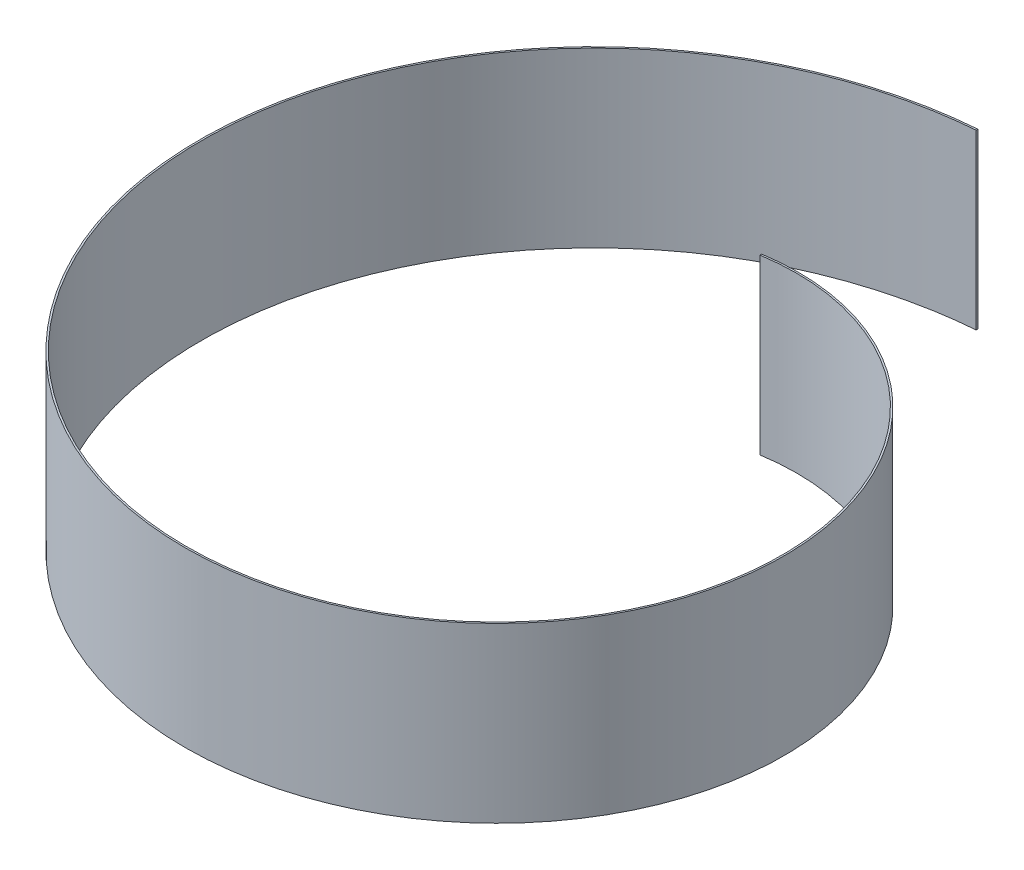
SolidWorks part; units mm, degrees
ref_plane "Front Plane" through (0, 0, 0) normal (0, 0, 1) x (1, 0, 0)
ref_plane "Top Plane" through (0, 0, 0) normal (0, 1, 0) x (1, 0, 0)
ref_plane "Right Plane" through (0, 0, 0) normal (1, 0, 0) x (0, 0, -1)
sketch "Sketch2" plane through (0, 0, 0) normal (0, 1, 0) x (1, 0, 0)
  circle A0 centre (0, 0) radius 250
  dimension "D1" = 500
curve "Helix/Spiral1"
sketch "Sketch4" plane through (0, 0, 0) normal (1, 0, 0) x (0, 0, -1)
  line L1 (250, 0) -> (248, 0)
  line L2 (250, 0) -> (250, 200)
  line L3 (250, 200) -> (248, 200)
  line L4 (248, 0) -> (248, 200)
  dimension "D1" = 250
  dimension "D2" = 2
  dimension "D3" = 200
sweep "Sweep1" add profiles "Sketch4" path "Helix/Spiral1"
sketch3d "3DSketch1"
  line L0 (0, 0, 0) -> (0, 273.3614, 0) construction
